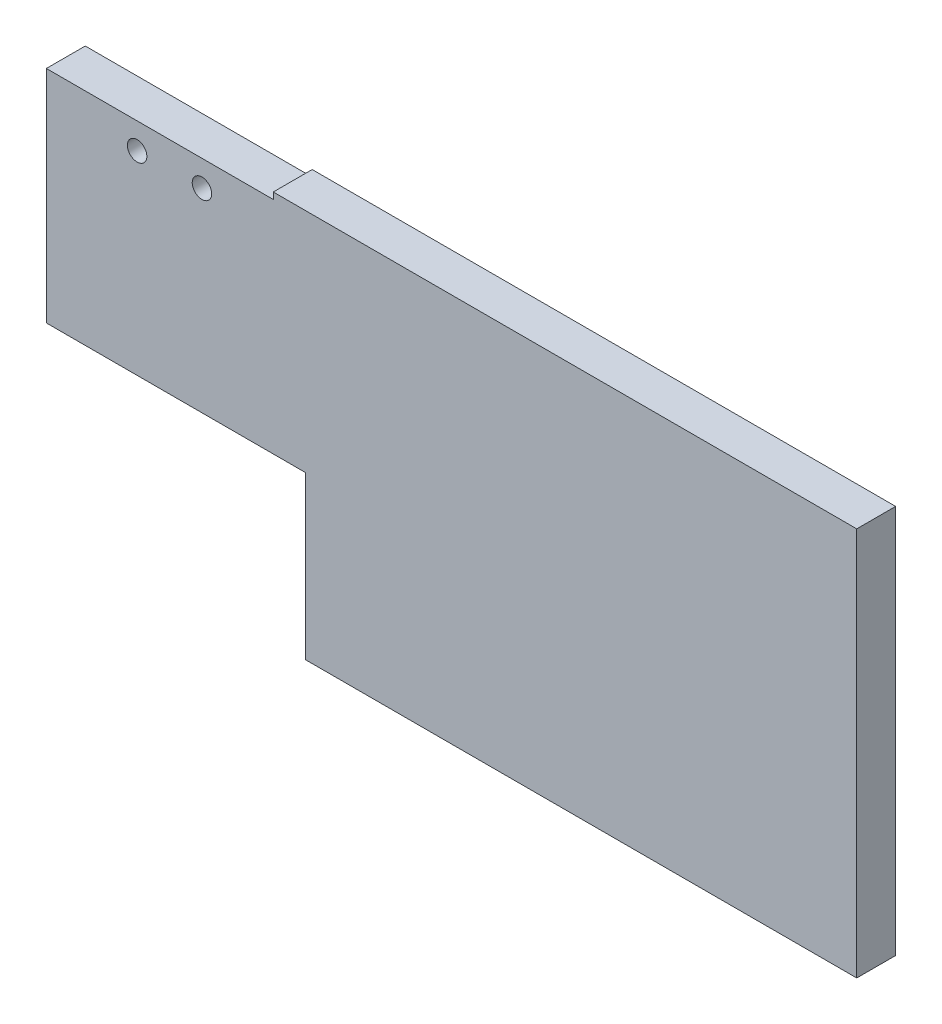
SolidWorks part; units mm, degrees
ref_plane "Plan de face" through (0, 0, 0) normal (0, 0, 1) x (1, 0, 0)
ref_plane "Plan de dessus" through (0, 0, 0) normal (0, 1, 0) x (1, 0, 0)
ref_plane "Plan de droite" through (0, 0, 0) normal (1, 0, 0) x (0, 0, -1)
sketch "Esquisse1" plane through (0, 0, 0) normal (0, 0, 1) x (1, 0, 0)
  line L0 (-36.7604, 24.4314) -> (-9.1915, 24.4314) construction
  line L1 (-45.6768, 29.4314) -> (79.3232, 29.4314)
  line L2 (-45.6768, 29.4314) -> (-45.6768, -30.5686)
  line L3 (-45.6768, -30.5686) -> (79.3232, -30.5686)
  line L4 (79.3232, 29.4314) -> (79.3232, -30.5686)
  circle A0 centre (-31.6768, 24.4314) radius 1.5
  circle A1 centre (-21.6768, 24.4314) radius 1.5
  dimension "D3" = 3
  dimension "D4" = 3
  dimension "D5" = 5
  dimension "D1" = 60
  dimension "D2" = 125
  dimension "D6" = 10
  dimension "D7" = 14
extrude "Boss.-Extru.1" add sketch "Esquisse1" along normal blind 6
sketch "Esquisse2" plane through (0, 0, 6) normal (0, 0, 1) x (1, 0, 0)
  line L0 (79.3232, 29.4314) -> (-45.6768, 29.4314) construction
  line L1 (-45.6768, -30.5686) -> (-5.6768, -30.5686)
  line L2 (-45.6768, -30.5686) -> (-45.6768, -5.5686)
  line L3 (-45.6768, -5.5686) -> (-5.6768, -5.5686)
  line L4 (-5.6768, -30.5686) -> (-5.6768, -5.5686)
  line L5 (-10.6768, 29.4314) -> (-45.6768, 29.4314)
  line L6 (-10.6768, 29.4314) -> (-10.6768, 28.4314)
  line L7 (-10.6768, 28.4314) -> (-45.6768, 28.4314)
  line L8 (-45.6768, 29.4314) -> (-45.6768, 28.4314)
  line L9 (-45.6768, 29.4314) -> (-45.6768, -30.5686) construction
  dimension "D1" = 40
  dimension "D2" = 25
  dimension "D3" = 1
  dimension "D4" = 35
extrude "Enlèv. mat.-Extru.1" cut sketch "Esquisse2" against normal blind 6
